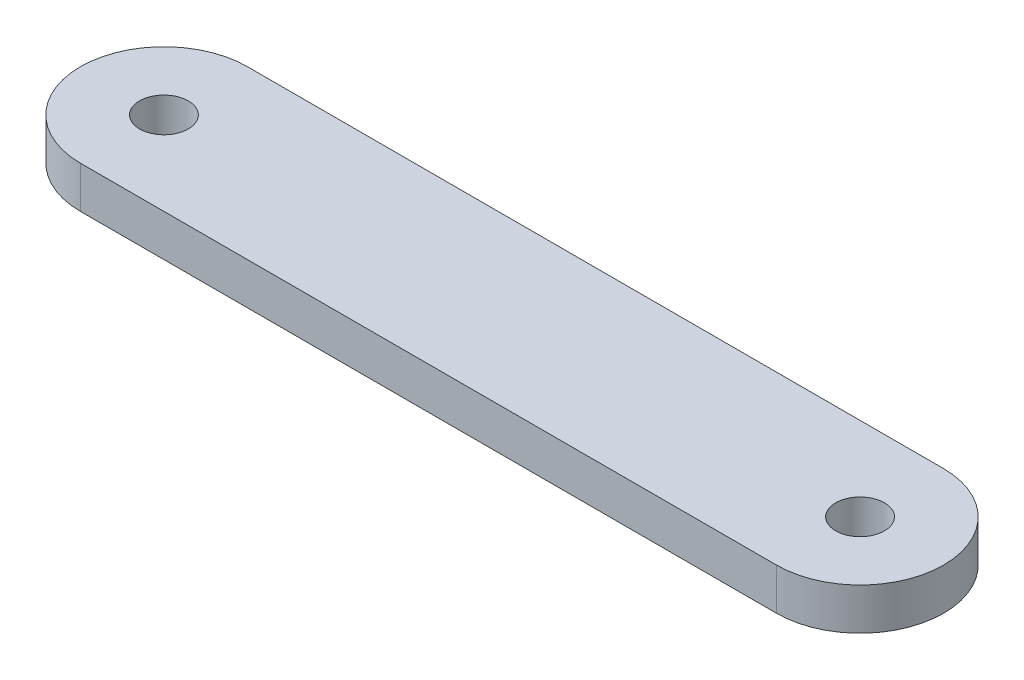
SolidWorks part; units mm, degrees
ref_plane "前基準面" through (0, 0, 0) normal (0, 0, 1) x (1, 0, 0)
ref_plane "上基準面" through (0, 0, 0) normal (0, 1, 0) x (1, 0, 0)
ref_plane "右基準面" through (0, 0, 0) normal (1, 0, 0) x (0, 0, -1)
sketch "草圖1" plane through (0, 0, 0) normal (0, 1, 0) x (1, 0, 0)
  line L0 (0, 0) -> (50, 0) construction
  line L1 (-1.65, 0) -> (1.65, 0) construction
  line L2 (0, 6) -> (50, 6)
  line L3 (0, -6) -> (50, -6)
  arc A0 (0, 6) -> (0, -6) centre (0, 0) ccw
  arc A1 (50, -6) -> (50, 6) centre (50, 0) ccw
  circle A2 centre (0, 0) radius 1.75
  circle A3 centre (50, 0) radius 1.75
  point P5 (25, 0)
  dimension "D3" = 3.5
  dimension "D4" = 3.5
  dimension "D1" = 50
  dimension "D2" = 12
extrude "填料-伸長1" add sketch "草圖1" along normal blind 3
